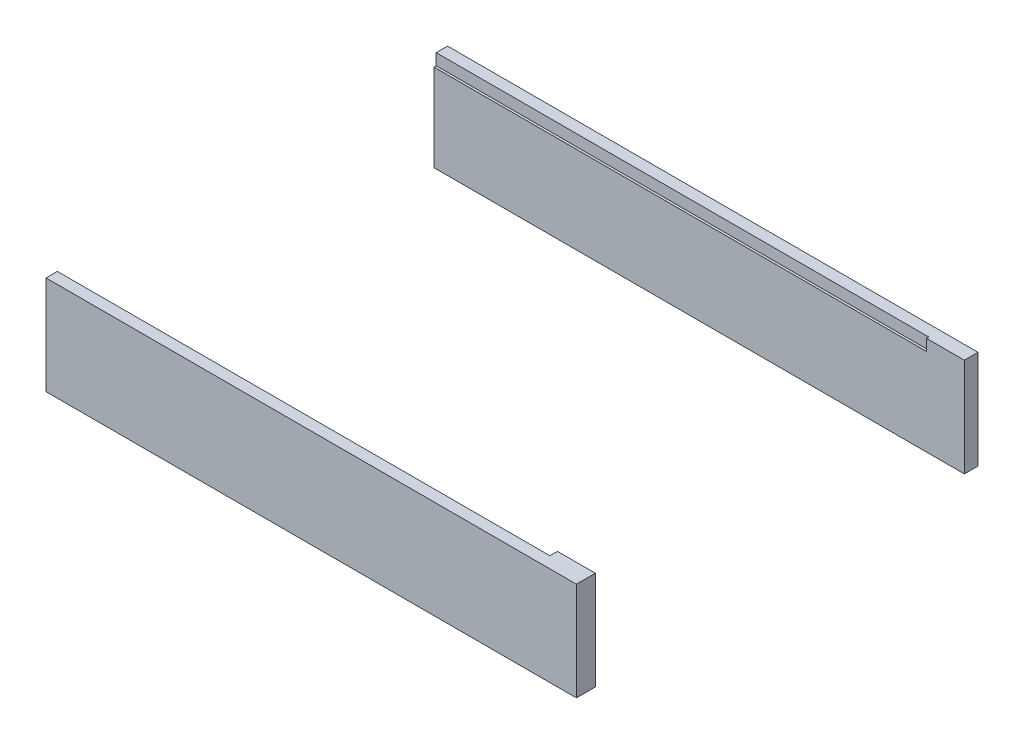
SolidWorks part; units mm, degrees
ref_plane "Front Plane" through (0, 0, 0) normal (0, 0, 1) x (1, 0, 0)
ref_plane "Top Plane" through (0, 0, 0) normal (0, 1, 0) x (1, 0, 0)
ref_plane "Right Plane" through (0, 0, 0) normal (1, 0, 0) x (0, 0, -1)
sketch "Sketch3" plane through (0, 0, 0) normal (0, 1, 0) x (1, 0, 0)
  line L1 (-39.8113, 2.7358) -> (30.1887, 2.7358)
  line L2 (-39.8113, 2.7358) -> (-39.8113, 0.9358)
  line L3 (-39.8113, 0.9358) -> (30.1887, 0.9358)
  line L4 (30.1887, 2.7358) -> (30.1887, 0.9358)
  line L5 (-39.8113, -50.2642) -> (30.1887, -50.2642)
  line L6 (-39.8113, -50.2642) -> (-39.8113, -47.7642)
  line L7 (-39.8113, -47.7642) -> (30.1887, -47.7642)
  line L8 (30.1887, -50.2642) -> (30.1887, -47.7642)
  point P10 (-39.8113, -49.0142)
  dimension "D1" = 70
  dimension "D2" = 1.8
  dimension "D3" = 2.5
  dimension "D4" = 53
  dimension "D5" = 0
extrude "Boss-Extrude1" add sketch "Sketch3" along normal blind 13
sketch "Sketch4" plane through (0, 13, 0) normal (0, 1, 0) x (1, 0, 0)
  line L1 (-39.8113, -47.7642) -> (25.1887, -47.7642)
  line L2 (-39.8113, -47.7642) -> (-39.8113, -48.7642)
  line L3 (-39.8113, -48.7642) -> (25.1887, -48.7642)
  line L4 (25.1887, -47.7642) -> (25.1887, -48.7642)
  dimension "D1" = 1
  dimension "D2" = 65
extrude "Cut-Extrude1" cut sketch "Sketch4" against normal blind 1.5
sketch "Sketch5" plane through (0, 13, 0) normal (0, 1, 0) x (1, 0, 0)
  line L1 (-39.8113, 0.9358) -> (25.1887, 0.9358)
  line L2 (-39.8113, 0.9358) -> (-39.8113, 1.2358)
  line L3 (-39.8113, 1.2358) -> (25.1887, 1.2358)
  line L4 (25.1887, 0.9358) -> (25.1887, 1.2358)
  dimension "D1" = 65
  dimension "D2" = 0.3
extrude "Cut-Extrude2" cut sketch "Sketch5" against normal blind 1.5
